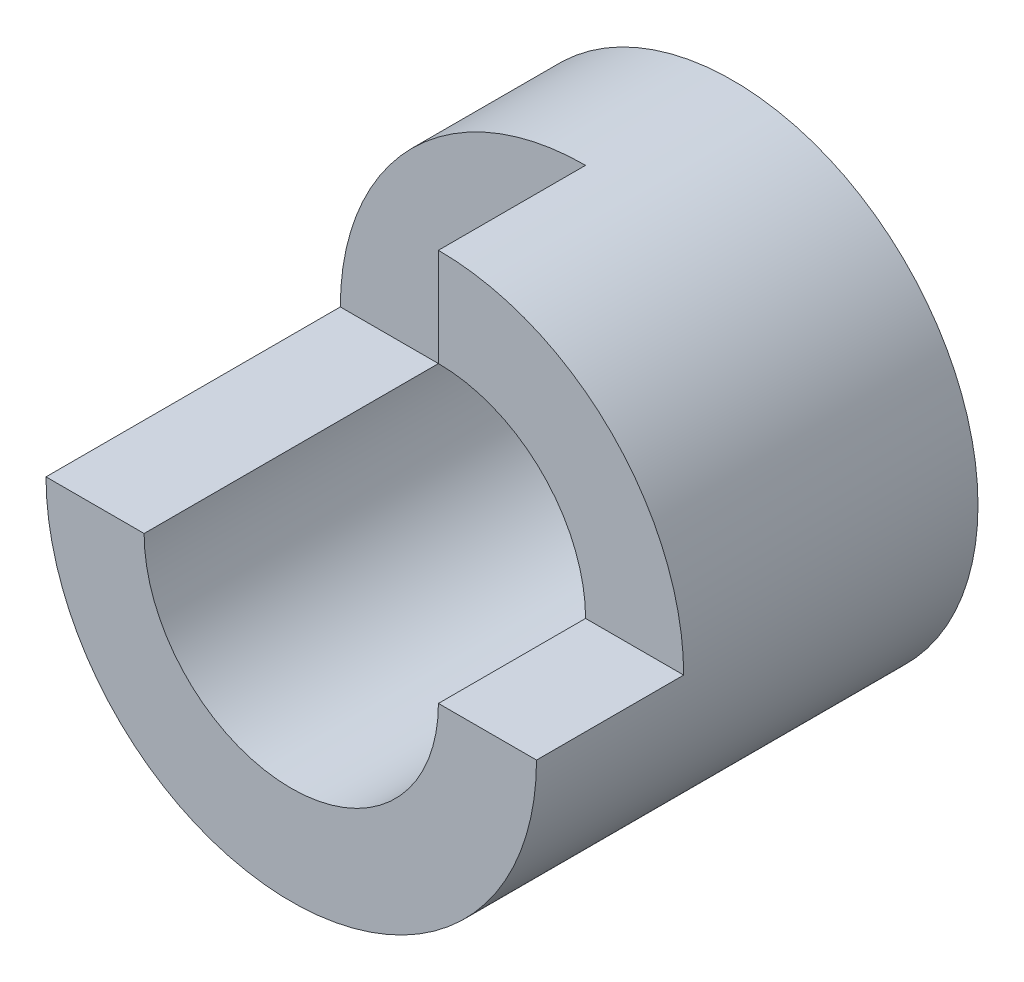
SolidWorks part; units mm, degrees
ref_plane "Front" through (0, 0, 0) normal (0, 0, 1) x (1, 0, 0)
ref_plane "Top" through (0, 0, 0) normal (0, 1, 0) x (1, 0, 0)
ref_plane "Right" through (0, 0, 0) normal (1, 0, 0) x (0, 0, -1)
sketch "Sketch1" plane through (0, 0, 0) normal (0, 0, 1) x (1, 0, 0)
  circle A0 centre (0, 0) radius 5
  circle A1 centre (0, 0) radius 3
  dimension "D1" = 6
  dimension "D2" = 10
extrude "Boss-Extrude1" add sketch "Sketch1" along normal blind 9
sketch "Sketch2" plane through (0, 0, 0) normal (0, 1, 0) x (1, 0, 0)
  line L0 (-5, -3) -> (0, -3)
  line L1 (-5, 0) -> (-5, -9) construction
  line L2 (0, -3) -> (0, -6)
  line L3 (0, -6) -> (3.187, -6)
  line L4 (3.187, -6) -> (6.3914, -6)
  line L5 (6.3914, -6) -> (6.3914, -9.6985)
  line L6 (6.3914, -9.6985) -> (-6.0431, -9.6985)
  line L7 (-6.0431, -9.6985) -> (-6.0431, -2.3144)
  line L8 (-6.0431, -2.3144) -> (-5, -2.4363)
  line L9 (-5, -2.4363) -> (-5, -3)
  line L10 (5, 0) -> (-5, 0) construction
  dimension "D1" = 5
  dimension "D2" = 3
  dimension "D3" = 3
extrude "Cut-Extrude1" cut sketch "Sketch2" along normal blind 9
